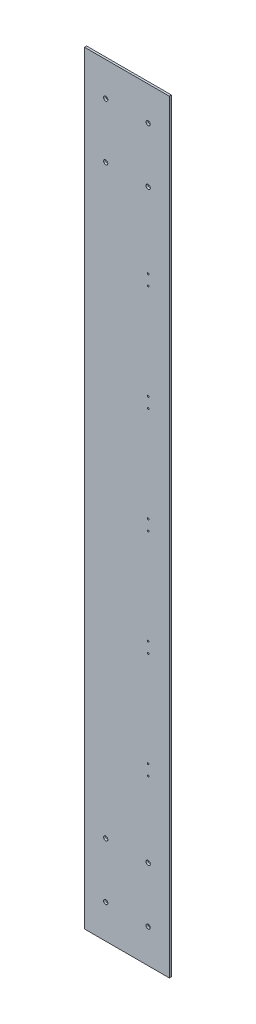
SolidWorks part; units mm, degrees
ref_plane "Front Plane" through (0, 0, 0) normal (0, 0, 1) x (1, 0, 0)
ref_plane "Top Plane" through (0, 0, 0) normal (0, 1, 0) x (1, 0, 0)
ref_plane "Right Plane" through (0, 0, 0) normal (1, 0, 0) x (0, 0, -1)
sketch "Sketch2" plane through (0, 0, 0) normal (0, 0, 1) x (1, 0, 0)
  line L2 (-100, 900) -> (-100, -900)
  line L3 (-100, -900) -> (100, -900)
  line L4 (100, -900) -> (100, 900)
  line L5 (100, 900) -> (-100, 900)
  dimension "D9" = 1800
  dimension "D10" = 200
extrude "Boss-Extrude1" add sketch "Sketch2" along normal blind 5 contours L2 L3 L4 L5
sketch "Sketch3" plane through (0, 0, 5) normal (0, 0, 1) x (1, 0, 0)
  circle A0 centre (-50, -690) radius 5
  circle A1 centre (50, -690) radius 5
  circle A2 centre (-50, -820) radius 5
  circle A3 centre (50, -820) radius 5
  circle A9 centre (50, 820) radius 5
  circle A10 centre (-50, 820) radius 5
  circle A11 centre (50, 690) radius 5
  circle A12 centre (-50, 690) radius 5
  circle A13 centre (50, 512.5) radius 2
  circle A14 centre (50, 487.5) radius 2
  circle A15 centre (50, 262.5) radius 2
  circle A16 centre (50, 237.5) radius 2
  circle A17 centre (50, 12.5) radius 2
  circle A18 centre (50, -12.5) radius 2
  circle A19 centre (50, -237.5) radius 2
  circle A20 centre (50, -262.5) radius 2
  circle A21 centre (50, -487.5) radius 2
  circle A22 centre (50, -512.5) radius 2
extrude "Cut-Extrude1" cut sketch "Sketch3" against normal blind 5
